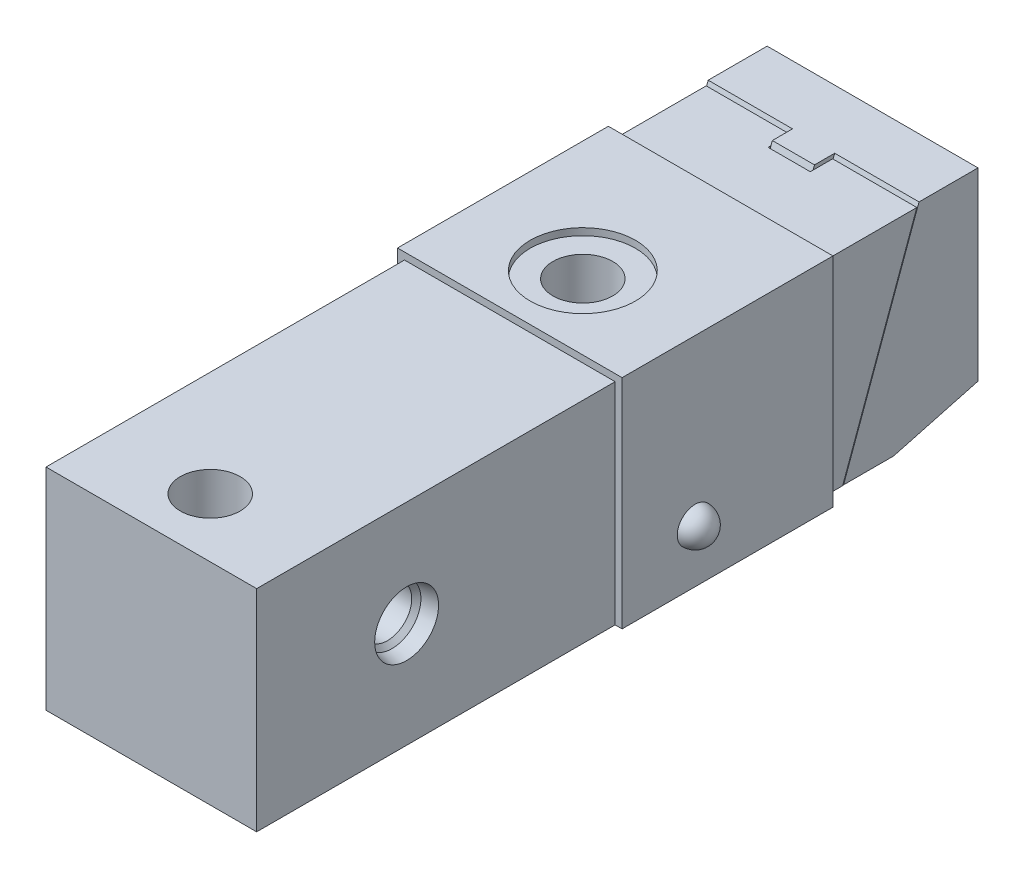
SolidWorks part; units mm, degrees
material "Alloy Steel"
ref_plane "Front Plane" through (0, 0, 0) normal (0, 0, 1) x (1, 0, 0)
ref_plane "Top Plane" through (0, 0, 0) normal (0, 1, 0) x (1, 0, 0)
ref_plane "Right Plane" through (0, 0, 0) normal (1, 0, 0) x (0, 0, -1)
sketch "Sketch1" plane through (0, 0, 0) normal (1, 0, 0) x (0, 0, -1)
  line L0 (0, 0) -> (73.9902, 0)
  line L1 (73.9902, 0) -> (73.9902, 29.972)
  line L2 (73.9902, 29.972) -> (0, 29.972)
  line L3 (0, 29.972) -> (0, 0)
  dimension "D1" = 29.972
  dimension "D2" = 73.9902
extrude "Extrude1" add sketch "Sketch1" along normal mid plane 29.972
sketch "Sketch11" plane through (0, 0, 0) normal (1, 0, 0) x (0, 0, -1)
  line L0 (94.2264, 30.5161) -> (102.616, 30.5161)
  line L1 (102.616, 30.5161) -> (102.616, 4.2314)
  line L2 (102.616, 4.2314) -> (90.616, 1.016)
  line L3 (90.616, 1.016) -> (83.4892, 1.016)
  line L4 (83.4892, 1.016) -> (94.2264, 30.5161)
  line L5 (0, 29.972) -> (0, 0) construction
  line L6 (0, 0) -> (73.9902, 0) construction
  dimension "D1" = 15
  dimension "D2" = 3.2154
  dimension "D3" = 8.3896
  dimension "D4" = 20
  dimension "D5" = 102.616
  dimension "D6" = 1.016
  dimension "D7" = 29.5001
extrude "Extrude4" add sketch "Sketch11" along normal mid plane 29.9999 separate body
sketch "Sketch12" plane through (0, 0, 0) normal (1, 0, 0) x (0, 0, -1)
  line L0 (94.2264, 30.5161) -> (83.4892, 1.016)
  line L1 (83.4892, 1.016) -> (80.6159, 1.016)
  line L2 (80.6159, 1.016) -> (91.3531, 30.5161)
  line L3 (91.3531, 30.5161) -> (94.2264, 30.5161)
  line L4 (102.616, 30.5161) -> (94.2264, 30.5161) construction
  dimension "D1" = 2.7
extrude "Extrude5" add sketch "Sketch12" along normal mid plane 6
sketch "Sketch13" plane through (0, 0, 0) normal (1, 0, 0) x (0, 0, -1)
  line L0 (76.8573, 15.5161) -> (105.1345, 15.5161) construction
  line L1 (102.616, 19.5161) -> (97.8159, 19.5161)
  line L2 (102.616, 4.2314) -> (102.616, 30.5161) construction
  line L3 (97.8159, 19.5161) -> (97.8159, 17.6661)
  line L4 (97.8159, 17.6661) -> (95.8159, 17.6661)
  line L5 (95.8159, 17.6661) -> (95.8159, 24.0161)
  line L6 (95.8159, 24.0161) -> (76.7659, 24.0161)
  line L7 (76.7659, 24.0161) -> (76.7659, 15.5161)
  line L8 (76.7659, 15.5161) -> (102.616, 15.5161)
  line L9 (102.616, 15.5161) -> (102.616, 19.5161)
  line L10 (83.4892, 1.016) -> (90.616, 1.016) construction
  dimension "D1" = 14.5001
  dimension "D2" = 17
  dimension "D3" = 19.05
  dimension "D4" = 8
  dimension "D5" = 4.8001
  dimension "D6" = 6.8001
  dimension "D7" = 4.3
revolve "Cut-Revolve4" cut sketch "Sketch13" angle 360 about L0
sketch "Sketch14" plane through (0, 0, -97.8159) normal (0, 0, -1) x (-1, 0, 0)
  circle A0 centre (0, 15.5161) radius 3.5052
  dimension "D1" = 7.0104
extrude "Extrude6" add sketch "Sketch14" along normal blind 3.2479
sketch "Sketch15" plane through (0, 0, -101.0638) normal (0, 0, -1) x (-1, 0, 0)
  line L1 (2.3024, 15.5161) -> (1.1512, 17.51)
  line L2 (1.1512, 17.51) -> (-1.1512, 17.51)
  line L3 (-1.1512, 17.51) -> (-2.3024, 15.5161)
  line L4 (-2.3024, 15.5161) -> (-1.1512, 13.5222)
  line L5 (-1.1512, 13.5222) -> (1.1512, 13.5222)
  line L6 (1.1512, 13.5222) -> (2.3024, 15.5161)
  circle A0 centre (0, 15.5161) radius 1.9939 construction
  dimension "D1" = 3.9878
extrude "Cut-Extrude3" cut sketch "Sketch15" against normal up to surface (3.2479 mm away) up to face at (4, 15.5161, -97.8159)
sketch "Sketch2" plane through (0, 0, 0) normal (1, 0, 0) x (0, 0, -1)
  line L0 (77.9018, 29.972) -> (77.9018, 0.9652)
  line L1 (77.9018, 0.9652) -> (83.3716, 0.9652)
  line L2 (83.3716, 0.9652) -> (93.9292, 29.972)
  line L3 (93.9292, 29.972) -> (77.9018, 29.972)
  line L4 (73.9902, 29.972) -> (0, 29.972) construction
  line L5 (94.2264, 30.5161) -> (83.4892, 1.016) construction
  dimension "D1" = 29.0068
  dimension "D2" = 16.0274
  dimension "D3" = 0.0932
extrude "Extrude2" add sketch "Sketch2" against normal mid plane 29.972 separate body
sketch "Sketch3" plane through (0, 0, 0) normal (1, 0, 0) x (0, 0, -1)
  line L0 (90.7542, 29.972) -> (80.1966, 0.9652)
  line L1 (90.7542, 29.972) -> (93.9292, 29.972)
  line L2 (93.9292, 29.972) -> (83.3716, 0.9652)
  line L3 (83.3716, 0.9652) -> (80.1966, 0.9652)
  line L4 (93.9292, 29.972) -> (77.9018, 29.972) construction
  line L5 (77.9018, 0.9652) -> (83.3716, 0.9652) construction
  line L6 (83.3716, 0.9652) -> (93.9292, 29.972) construction
  dimension "D1" = 3.175
extrude "Cut-Extrude1" cut sketch "Sketch3" against normal mid plane 5.9944
sketch "Sketch4" plane through (0, 0, 0) normal (0, -1, 0) x (1, 0, 0)
  line L0 (14.986, 0) -> (-14.986, 0) construction
  circle A0 centre (0, -8.382) radius 4.2545
  circle A1 centre (0, -61.3918) radius 4.2545
  dimension "D1" = 8.509
  dimension "D2" = 53.0098
  dimension "D3" = 8.382
extrude "Cut-Extrude2" cut sketch "Sketch4" against normal up to next (29.972 mm away)
hole_wizard "Hole1" positions "Sketch17" profile "Sketch16" legacy
sketch "Sketch17" plane through (0, 0, 0) normal (0, -1, 0) x (1, 0, 0)
  line L0 (0, 0) -> (0, -63.3687) construction
  line L1 (14.986, 0) -> (-14.986, 0) construction
  point P0 (-11.049, -8.382)
  point P8 (-11.049, -67.3862)
  point P12 (11.049, -8.382)
  point P13 (11.049, -67.3862)
  dimension "D1" = 11.049
  dimension "D2" = 8.382
  dimension "D3" = 59.0042
sketch "Sketch16" plane through (-11.049, 0, -8.382) normal (1, 0, 0) x (0, 0, -1)
  line L0 (0, 0) -> (0, 7.5993)
  line L1 (0, 7.5993) -> (2.5019, 6.096)
  line L2 (2.5019, 6.096) -> (2.5019, 0)
  line L4 (2.5019, 0) -> (0, 0)
  line L6 (0, 7.5993) -> (-2.5019, 6.096) construction
  line L7 (0, -4.2442) -> (0, 117.3081) construction
  dimension "Diameter" = 5.0038
  dimension "Depth" = 6.096
  dimension "Drill Angle" = 118
ref_plane "Plane14" through (0, 14.986, 0) normal (0, -1, 0) x (1, 0, 0)
sketch "S2D0001" plane through (14.986, 14.986, -21.336) normal (0, -1, 0) x (0, 0, -1)
  line L0 (0, 0) -> (4.5466, 0)
  line L1 (4.5466, 0) -> (4.1066, -2.0701)
  line L2 (4.1066, -2.0701) -> (3.4544, -2.7223)
  line L3 (3.4544, -2.7223) -> (3.4544, -15.24)
  line L4 (3.4544, -15.24) -> (0, -15.24)
  line L5 (0, -15.24) -> (0, 0)
  line L6 (0, -25.3864) -> (0, 0.762) construction
  line L7 (-21.336, 0) -> (52.6542, 0) construction
  circle A0 centre (-12.954, -14.986) radius 4.2545 construction
  point P10 (0, 0)
  dimension "D2" = 12.954
  dimension "D1" = 15.24
  dimension "D3" = 6.9088
  dimension "D4" = 9.0932
  dimension "D5" = 2.0701
  dimension "D6" = 12
  dimension "D7" = 45
revolve "Cut-Revolve2" cut sketch "S2D0001" angle 360 about L6
mirror "Mirror1" about plane through (0, 0, 0) normal (1, 0, 0) of "Cut-Revolve2"
sketch "Sketch19" plane through (0, 0, 0) normal (1, 0, 0) x (0, 0, -1)
  line L0 (21.336, 14.986) -> (21.336, -8.8821) construction
  line L1 (25.654, 0) -> (25.654, 1.5875)
  line L2 (0, 0) -> (73.9902, 0) construction
  line L3 (25.654, 1.5875) -> (23.8379, 1.5875)
  line L4 (23.8379, 1.5875) -> (23.8379, 14.986)
  line L5 (23.8379, 14.986) -> (21.336, 14.986)
  line L6 (21.336, 14.986) -> (21.336, 0)
  line L7 (21.336, 0) -> (25.654, 0)
  dimension "D1" = 1.5875
  dimension "D2" = 5.0038
  dimension "D3" = 8.636
revolve "Cut-Revolve5" cut sketch "Sketch19" angle 360 about L0
sketch "Sketch8" plane through (0, 0, 0) normal (1, 0, 0) x (0, 0, -1)
  line L0 (21.336, -0.5194) -> (21.336, 1.6878) construction
  line L1 (0, 0) -> (73.9902, 0) construction
  line L2 (18.8341, 12.6041) -> (18.8341, 1.5875) construction
  line L3 (23.8379, 1.5875) -> (23.8379, 12.6041) construction
  circle A0 centre (24.6507, 0.5842) radius 1.0033
  dimension "D1" = 2.0066
  dimension "D2" = 6.6294
  dimension "D3" = 0.5842
revolve "Revolve1" add sketch "Sketch8" angle 360 about L0
ref_plane "Plane15" through (0, 0, -81.0006) normal (0, 0, -1) x (-1, 0, 0)
sketch "Sketch9" plane through (0, 0, -81.0006) normal (0, 0, -1) x (-1, 0, 0)
  line L0 (14.986, 29.972) -> (14.986, 0)
  line L1 (14.986, 29.972) -> (-14.986, 29.972)
  line L2 (-14.986, 29.972) -> (-14.986, 0)
  line L3 (-14.986, 0) -> (-15.9766, 0)
  line L4 (-15.9766, 0) -> (-15.9766, 30.9626)
  line L5 (-15.9766, 30.9626) -> (15.9766, 30.9626)
  line L6 (15.9766, 30.9626) -> (15.9766, 0)
  line L7 (15.9766, 0) -> (14.986, 0)
  line L8 (14.986, 29.972) -> (14.986, 0) construction
  line L9 (-14.986, 29.972) -> (14.986, 29.972) construction
  line L10 (-14.986, 29.972) -> (-14.986, 0) construction
  line L11 (-14.986, 0) -> (14.986, 0) construction
  dimension "D1" = 0.9906
  dimension "D2" = 0.9906
extrude "Extrude3" add sketch "Sketch9" against normal blind 29.9974 separate body
ref_plane "Plane16" through (0, 7.62, 0) normal (0, -1, 0) x (1, 0, 0)
sketch "Sketch10" plane through (0, 7.62, -83.7438) normal (0, 1, 0) x (1, 0, 0)
  line L0 (15.9766, -19.812) -> (15.9766, -22.352)
  line L1 (-15.9766, -19.812) -> (-15.9766, -22.352)
  line L2 (15.9766, -22.352) -> (18.5166, -22.352)
  line L3 (-18.5166, -22.352) -> (-15.9766, -22.352)
  line L4 (-20.3683, -22.352) -> (20.3683, -22.352) construction
  line L5 (-15.9766, -32.7406) -> (-15.9766, -2.7432) construction
  line L6 (15.9766, -32.7406) -> (15.9766, -2.7432) construction
  arc A0 (18.5166, -22.352) -> (15.9766, -19.812) centre (15.9766, -22.352) ccw
  arc A1 (-15.9766, -19.812) -> (-18.5166, -22.352) centre (-15.9766, -22.352) ccw
  dimension "D2" = 2.54
  dimension "D1" = 53.0098
revolve "Revolve2" add sketch "Sketch10" angle 360 about L4
sketch "Sketch18" plane through (0, 30.9626, 0) normal (0, 1, 0) x (1, 0, 0)
  circle A0 centre (0, 61.3918) radius 7.493
  dimension "D1" = 14.986
extrude "Cut-Extrude4" cut sketch "Sketch18" against normal up to surface (0.9906 mm away) up to face at (0, 29.972, -65.6463)
